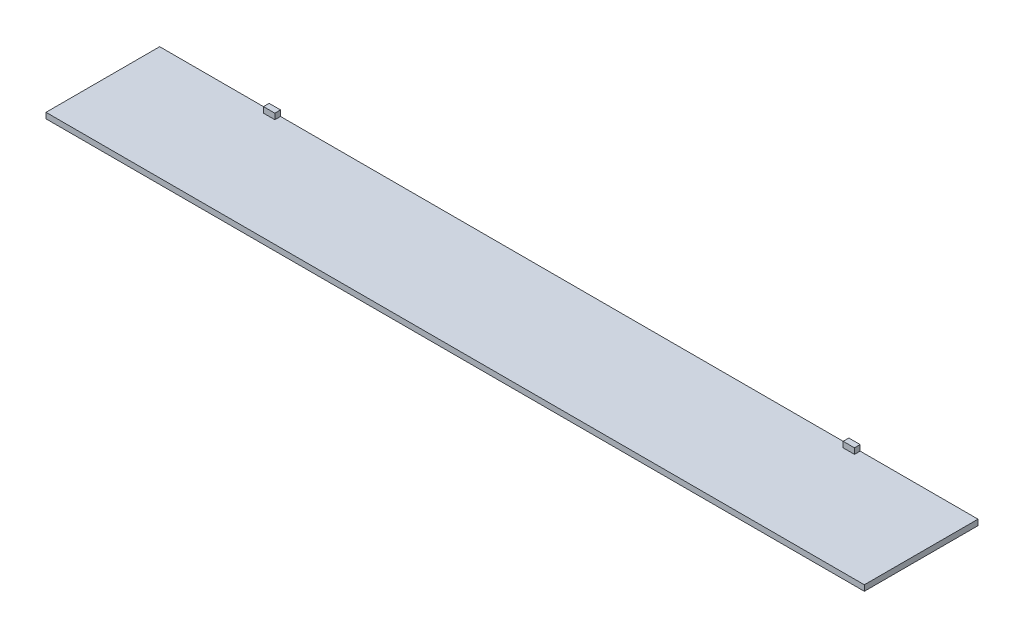
SolidWorks part; units mm, degrees
ref_plane "Front Plane" through (0, 0, 0) normal (0, 0, 1) x (1, 0, 0)
ref_plane "Top Plane" through (0, 0, 0) normal (0, 1, 0) x (1, 0, 0)
ref_plane "Right Plane" through (0, 0, 0) normal (1, 0, 0) x (0, 0, -1)
sketch "Sketch1" plane through (0, 0, 0) normal (0, 1, 0) x (1, 0, 0)
  line L1 (-720, -100) -> (720, -100)
  line L2 (-720, -100) -> (-720, 100)
  line L3 (-720, 100) -> (720, 100)
  line L4 (720, -100) -> (720, 100)
  line L5 (-720, -100) -> (720, 100) construction
  line L6 (-720, 100) -> (720, -100) construction
  point P1 (0, 0)
  dimension "D1" = 200
  dimension "D2" = 1440
extrude "Boss-Extrude1" add sketch "Sketch1" along normal blind 10
sketch "Sketch3" plane through (0, 10, 0) normal (0, 1, 0) x (1, 0, 0)
  line L0 (-507.34, 90) -> (-527.34, 90)
  line L1 (-507.34, 90) -> (-507.34, 100)
  line L2 (-507.34, 100) -> (-527.34, 100)
  line L3 (-527.34, 90) -> (-527.34, 100)
  line L4 (-507.34, 90) -> (-527.34, 100) construction
  line L5 (-507.34, 100) -> (-527.34, 90) construction
  line L6 (-720, 100) -> (-720, -100) construction
  line L7 (720, 100) -> (-720, 100) construction
  line L8 (512.66, 90) -> (492.66, 90)
  line L9 (512.66, 90) -> (512.66, 100)
  line L10 (512.66, 100) -> (492.66, 100)
  line L11 (492.66, 90) -> (492.66, 100)
  line L12 (512.66, 90) -> (492.66, 100) construction
  line L13 (512.66, 100) -> (492.66, 90) construction
  point P0 (-517.34, 95)
  point P9 (502.66, 95)
  point P14 (492.66, 95)
  point P15 (-507.34, 95)
  dimension "D1" = 10
  dimension "D2" = 20
  dimension "D3" = 212.66
  dimension "D4" = 0
  dimension "D5" = 20
  dimension "D6" = 1000
  dimension "D7" = 0
extrude "Boss-Extrude3" add sketch "Sketch3" along normal blind 10
